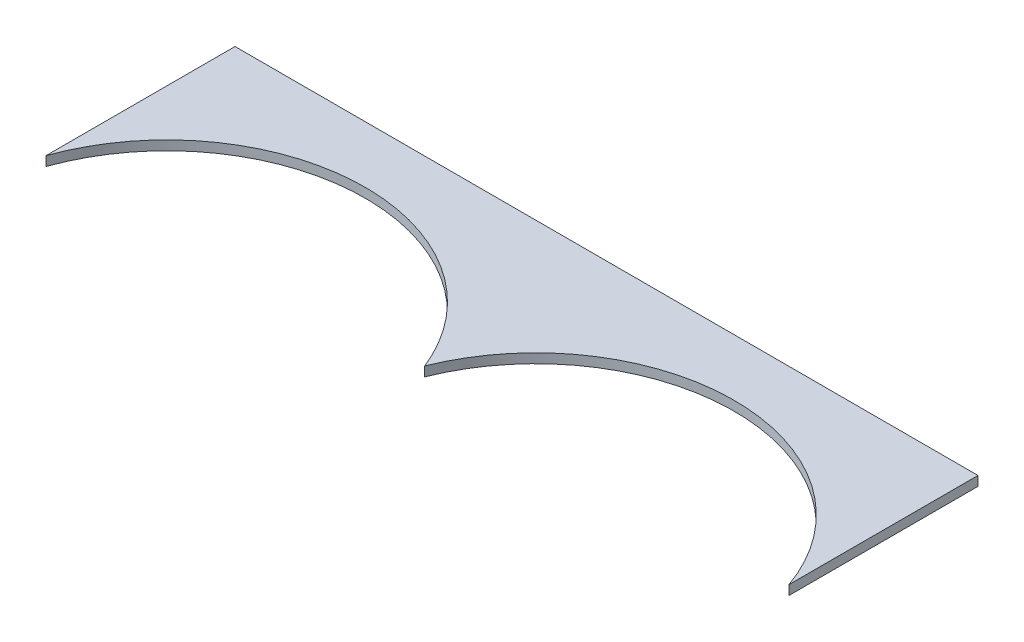
SolidWorks part; units mm, degrees
ref_plane "Plan de face" through (0, 0, 0) normal (0, 0, 1) x (1, 0, 0)
ref_plane "Plan de dessus" through (0, 0, 0) normal (0, 1, 0) x (1, 0, 0)
ref_plane "Plan de droite" through (0, 0, 0) normal (1, 0, 0) x (0, 0, -1)
sketch "Esquisse1" plane through (0, 0, 0) normal (0, 1, 0) x (1, 0, 0)
  line L1 (-72.2115, 21.3275) -> (85.0193, 21.3275)
  line L2 (-72.2115, 21.3275) -> (-72.2115, -18.6725)
  line L4 (85.0193, 21.3275) -> (85.0193, -18.6725)
  arc A0 (-72.2115, -18.6725) -> (6.4039, -17.1678) centre (-32.621, -32.6937) cw
  arc A1 (6.4039, -17.1678) -> (85.0193, -18.6725) centre (45.4288, -32.6937) cw
  dimension "D1" = 42
  dimension "D2" = 42
  dimension "D3" = 40
extrude "Boss.-Extru.1" add sketch "Esquisse1" along normal blind 2
